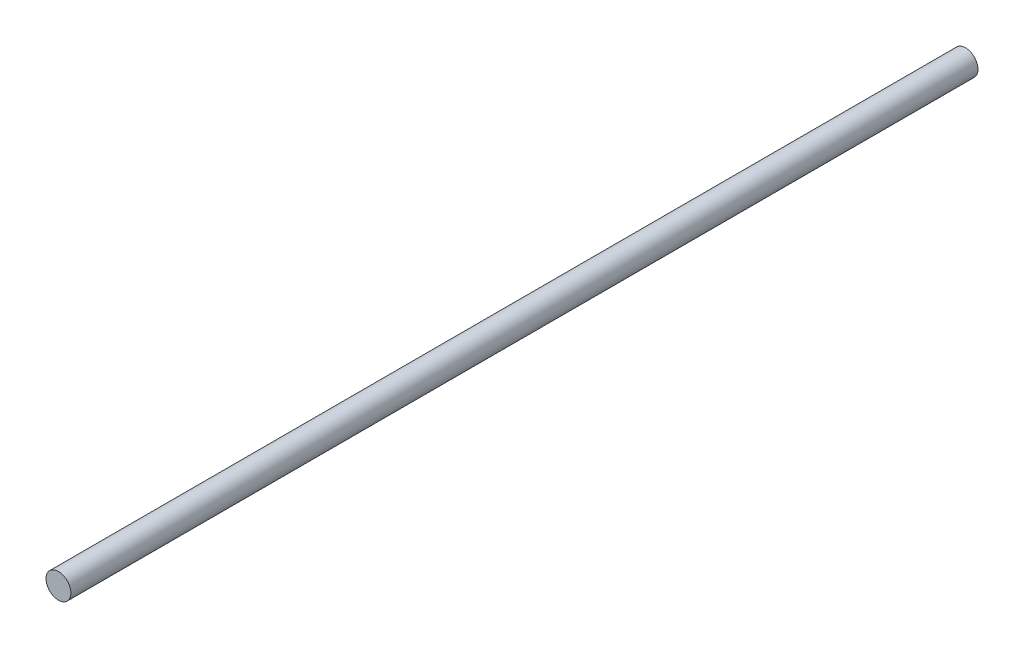
SolidWorks part; units mm, degrees
material "Stainless Steel (ferritic)"
ref_plane "Front Plane" through (0, 0, 0) normal (0, 0, 1) x (1, 0, 0)
ref_plane "Top Plane" through (0, 0, 0) normal (0, 1, 0) x (1, 0, 0)
ref_plane "Right Plane" through (0, 0, 0) normal (1, 0, 0) x (0, 0, -1)
sketch "Sketch1" plane through (0, 0, 0) normal (0, 0, 1) x (1, 0, 0)
  circle A0 centre (0, 0) radius 0.7
  dimension "D1" = 1.4
extrude "Boss-Extrude1" add sketch "Sketch1" along normal blind 51
